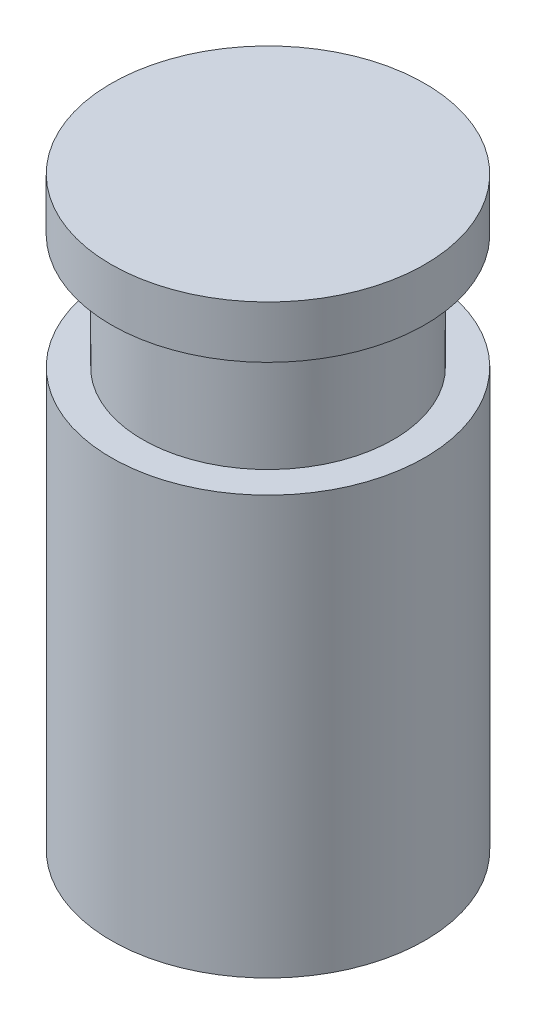
SolidWorks part; units mm, degrees
ref_plane "Front Plane" through (0, 0, 0) normal (0, 0, 1) x (1, 0, 0)
ref_plane "Top Plane" through (0, 0, 0) normal (0, 1, 0) x (1, 0, 0)
ref_plane "Right Plane" through (0, 0, 0) normal (1, 0, 0) x (0, 0, -1)
sketch "Sketch1" plane through (0, 0, 0) normal (0, 1, 0) x (1, 0, 0)
  circle A0 centre (0, 0) radius 6
extrude "Boss-Extrude1" add sketch "Sketch1" along normal blind 8 contours A0
sketch "Sketch3" plane through (0, 0, 0) normal (0, -1, 0) x (1, 0, 0)
  circle A0 centre (0, 0) radius 7.5
extrude "Boss-Extrude2" add sketch "Sketch3" along normal blind 20
sketch "Sketch4" plane through (0, 8, 0) normal (0, 1, 0) x (1, 0, 0)
  circle A0 centre (0, 0) radius 7.5
extrude "Boss-Extrude3" add sketch "Sketch4" against normal blind 2.5
